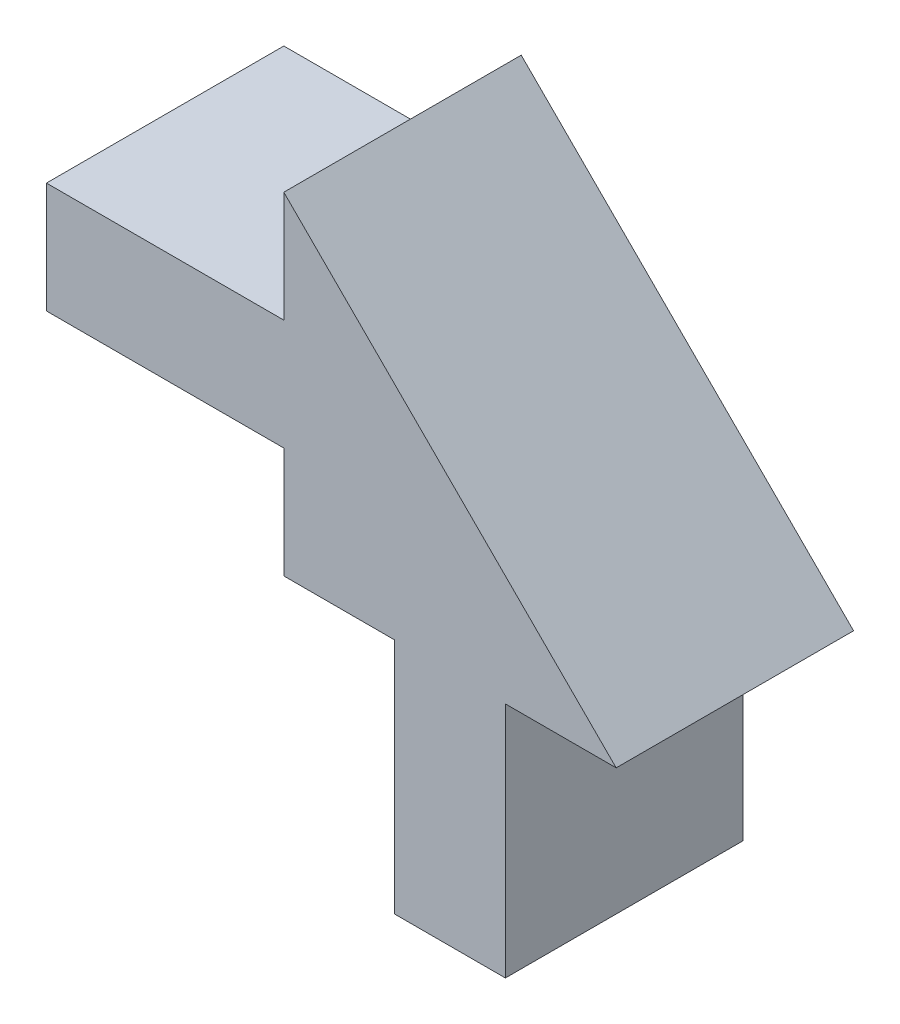
SolidWorks part; units mm, degrees
ref_plane "Front Plane" through (0, 0, 0) normal (0, 0, 1) x (1, 0, 0)
ref_plane "Top Plane" through (0, 0, 0) normal (0, 1, 0) x (1, 0, 0)
ref_plane "Right Plane" through (0, 0, 0) normal (1, 0, 0) x (0, 0, -1)
sketch "Sketch1" plane through (0, 0, 0) normal (0, 0, 1) x (1, 0, 0)
  line L0 (0, 8.89) -> (8.89, 0)
  line L1 (0, 0) -> (2.9633, 0)
  line L2 (0, 0) -> (0, 2.9633)
  line L3 (5.9267, 0) -> (8.89, 0)
  line L4 (0, 5.9267) -> (0, 8.89)
  line L5 (2.9633, 0) -> (2.9633, -6.35)
  line L6 (2.9633, -6.35) -> (5.9267, -6.35)
  line L7 (5.9267, 0) -> (5.9267, -6.35)
  line L8 (0, 5.9267) -> (-6.35, 5.9267)
  line L10 (0, 2.9633) -> (-6.35, 2.9633)
  line L11 (-6.35, 5.9267) -> (-6.35, 2.9633)
  dimension "D1" = 8.89
  dimension "D2" = 8.89
  dimension "D3" = 6.35
  dimension "D4" = 6.35
extrude "Boss-Extrude1" add sketch "Sketch1" along normal blind 6.35 contours L0 L3 L7 L6 L5 L1 L2 L10 L11 L8 L4
